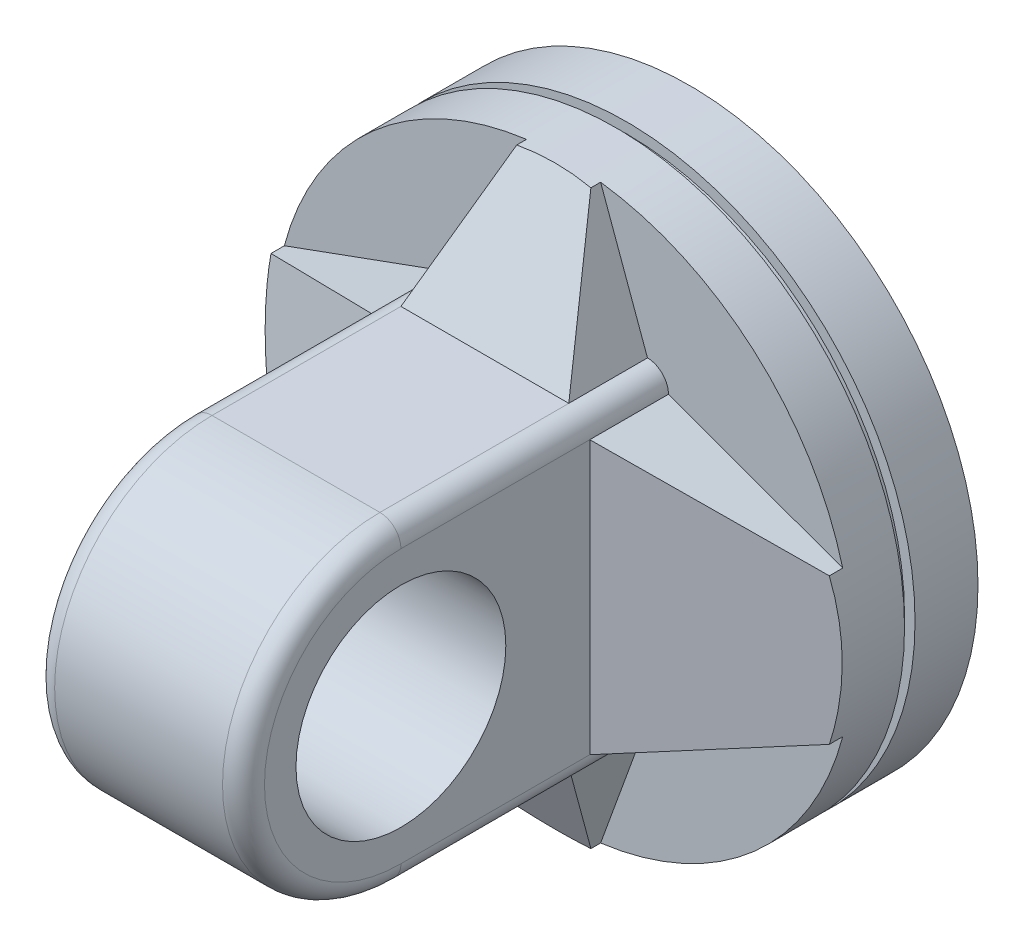
SolidWorks part; units mm, degrees
ref_plane "Front Plane" through (0, 0, 0) normal (0, 0, 1) x (1, 0, 0)
ref_plane "Top Plane" through (0, 0, 0) normal (0, 1, 0) x (1, 0, 0)
ref_plane "Right Plane" through (0, 0, 0) normal (1, 0, 0) x (0, 0, -1)
sketch "Sketch1" plane through (0, 0, 0) normal (0, 0, 1) x (1, 0, 0)
  circle A0 centre (0, 0) radius 275
  dimension "D1" = 550
extrude "Boss-Extrude1" add sketch "Sketch1" along normal blind 70
sketch "Sketch2" plane through (0, 0, 70) normal (0, 0, 1) x (1, 0, 0)
  circle A0 centre (0, 0) radius 275 construction
  circle A1 centre (0, 0) radius 275
  circle A2 centre (0, 0) radius 265
  dimension "D1" = 10
extrude "Cut-Extrude1" cut sketch "Sketch2" against normal blind 10
sketch "Sketch3" plane through (0, 0, 70) normal (0, 0, 1) x (1, 0, 0)
  circle A0 centre (0, 0) radius 275 construction
  circle A1 centre (0, 0) radius 275
extrude "Boss-Extrude2" add sketch "Sketch3" along normal blind 50
sketch "Sketch4" plane through (0, 0, 0) normal (1, 0, 0) x (0, 0, -1)
  circle A0 centre (-375, 0) radius 100
  circle A1 centre (-375, 0) radius 150
  dimension "D1" = 200
  dimension "D2" = 375
  dimension "D3" = 300
extrude "Boss-Extrude3" add sketch "Sketch4" along normal mid plane 200 separate body
sketch "Sketch6" plane through (0, 0, 0) normal (1, 0, 0) x (0, 0, -1)
  line L0 (-375, 150) -> (-120, 150)
  line L1 (-120, 275) -> (-120, -275) construction
  line L2 (-375, -150) -> (-120, -150)
  line L3 (-120, -150) -> (-120, 150)
  circle A0 centre (-375, 0) radius 150 construction
  arc A1 (-375, -150) -> (-375, 150) centre (-375, 0) ccw
extrude "Boss-Extrude4" add sketch "Sketch6" along normal mid plane 200
fillet "Fillet3" radius 20 6 edges at (100, 150, 247.5) (100, -150, 247.5) (-100, 150, 247.5) (-100, -150, 247.5) (-100, 0, 525) (100, 0, 525)
sketch "Sketch7" plane through (0, 0, 120) normal (0, 0, 1) x (1, 0, 0)
  line L0 (-80, -150) -> (-35.3333, -272.7207)
  line L1 (80, -150) -> (-80, -150) construction
  line L2 (0, -1000) -> (0, 49000) construction
  line L3 (-1000, 0) -> (49000, 0) construction
  line L4 (100, -130) -> (266.0571, -69.5602)
  line L5 (100, -130) -> (100, 130) construction
  line L6 (80, -150) -> (35.3333, -272.7207)
  line L7 (100, 130) -> (266.0571, 69.5602)
  line L8 (-100, -130) -> (-266.0571, -69.5602)
  line L9 (-100, 130) -> (-266.0571, 69.5602)
  line L10 (80, 150) -> (35.3333, 272.7207)
  line L11 (-80, 150) -> (-35.3333, 272.7207)
  arc A0 (-100, -130) -> (-80, -150) centre (-80, -130) ccw construction
  circle A1 centre (0, 0) radius 275
  circle A2 centre (0, 0) radius 275
  circle M8 centre (0, 0) radius 275
  line M9 (100, 130) -> (100, -130)
  line M11 (80, -150) -> (-80, -150)
  line M13 (-100, -130) -> (-100, 130)
  line M15 (-80, 150) -> (80, 150)
  dimension "D2" = 70
  dimension "D3" = 70
  dimension "D1" = 0
extrude "Boss-Extrude5" add sketch "Sketch7" along normal blind 75 contours L9 L8 M13 M8 | L7 L4 M9 M8 | L11 L10 M15 M8 | L6 L0 M11 M8
sketch "Sketch8" plane through (0, 0, 0) normal (0, 1, 0) x (1, 0, 0)
  line L4 (-300, -120) -> (-100, -195)
  line L5 (0, -1000) -> (0, 49000) construction
  line L7 (300, -120) -> (100, -195)
  line L9 (-100, -195) -> (-300, -195)
  line L10 (-300, -195) -> (-300, -120)
  line L11 (300, -120) -> (300, -195)
  line L12 (300, -195) -> (100, -195)
  dimension "D1" = 200
  dimension "D2" = 75
extrude "Cut-Extrude4" cut sketch "Sketch8" against normal mid plane 300
sketch "Sketch9" plane through (0, 0, 0) normal (1, 0, 0) x (0, 0, -1)
  line L0 (-195, 150) -> (-195, 290)
  line L1 (-195, 290) -> (-120, 290)
  line L2 (-120, 290) -> (-195, 150)
  line L3 (-1000, 0) -> (49000, 0) construction
  line L4 (-120, -290) -> (-195, -150)
  line L5 (-195, -150) -> (-195, -290)
  line L6 (-195, -290) -> (-120, -290)
  dimension "D1" = 75
  dimension "D2" = 140
extrude "Cut-Extrude5" cut sketch "Sketch9" against normal mid plane 175
